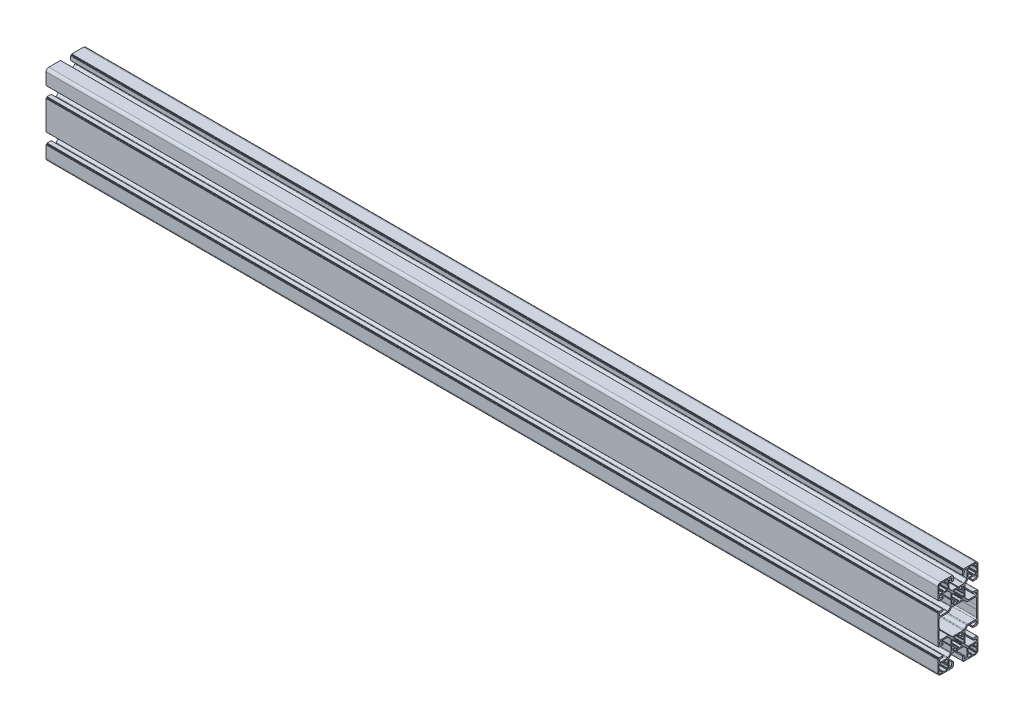
SolidWorks part; units mm, degrees
ref_plane "Спереди" through (0, 0, 0) normal (0, 0, 1) x (1, 0, 0)
ref_plane "Сверху" through (0, 0, 0) normal (0, 1, 0) x (1, 0, 0)
ref_plane "Справа" through (0, 0, 0) normal (1, 0, 0) x (0, 0, -1)
other "Центр тяжести"
sketch "Эскиз1" plane through (0, 0, 0) normal (0, 0, 1) x (1, 0, 0)
  line L0 (-35.8248, 14.5782) -> (-35.8248, 11.29)
  line L1 (-36.0902, 10.889) -> (-36.2238, 10.889)
  line L2 (-36.4238, 10.689) -> (-36.4238, 10.5554)
  line L3 (-36.8248, 10.29) -> (-40.1131, 10.29)
  line L4 (-40.3597, 10.4989) -> (-40.49, 11.2811)
  line L5 (-40.7366, 11.49) -> (-41.3131, 11.49)
  line L6 (-41.5597, 11.2811) -> (-41.69, 10.4989)
  line L7 (-41.9366, 10.29) -> (-44.8248, 10.29)
  line L8 (-45.2259, 10.5554) -> (-45.2259, 10.689)
  line L9 (-45.4259, 10.889) -> (-45.5595, 10.889)
  line L10 (-45.8248, 11.29) -> (-45.8248, 14.5948)
  line L11 (-45.6355, 14.8374) -> (-45.2142, 14.9427)
  line L12 (-45.0248, 15.1852) -> (-45.0248, 15.7948)
  line L13 (-45.2142, 16.0374) -> (-45.6355, 16.1427)
  line L14 (-45.8248, 16.3852) -> (-45.8248, 18.49)
  line L15 (-45.3992, 19.4567) -> (-45.1916, 19.4567)
  line L16 (-44.9916, 19.6567) -> (-44.9916, 19.8644)
  line L17 (-44.0248, 20.29) -> (-41.92, 20.29)
  line L18 (-41.6775, 20.1007) -> (-41.5722, 19.6794)
  line L19 (-41.3297, 19.49) -> (-40.72, 19.49)
  line L20 (-40.4775, 19.6794) -> (-40.3722, 20.1007)
  line L21 (-40.1297, 20.29) -> (-36.8248, 20.29)
  line L22 (-36.4238, 20.0247) -> (-36.4238, 19.8911)
  line L23 (-36.2238, 19.6911) -> (-36.0902, 19.6911)
  line L24 (-35.8248, 19.29) -> (-35.8248, 16.4018)
  line L25 (-36.0337, 16.1552) -> (-36.8159, 16.0248)
  line L26 (-37.0248, 15.7782) -> (-37.0248, 15.2018)
  line L27 (-36.8159, 14.9552) -> (-36.0337, 14.8248)
  line L28 (-40.1131, -12.31) -> (-36.8248, -12.31)
  line L29 (-36.4238, -12.5753) -> (-36.4238, -12.7089)
  line L30 (-36.2238, -12.9089) -> (-36.0902, -12.9089)
  line L31 (-35.8248, -13.31) -> (-35.8248, -16.5982)
  line L32 (-36.0337, -16.8448) -> (-36.8159, -16.9752)
  line L33 (-37.0248, -17.2218) -> (-37.0248, -17.7982)
  line L34 (-36.8159, -18.0448) -> (-36.0337, -18.1752)
  line L35 (-35.8248, -18.4218) -> (-35.8248, -21.31)
  line L36 (-36.0902, -21.711) -> (-36.2238, -21.711)
  line L37 (-36.4238, -21.911) -> (-36.4238, -22.0446)
  line L38 (-36.8248, -22.31) -> (-40.1297, -22.31)
  line L39 (-40.3722, -22.1206) -> (-40.4775, -21.6993)
  line L40 (-40.72, -21.51) -> (-41.3297, -21.51)
  line L41 (-41.5722, -21.6993) -> (-41.6775, -22.1206)
  line L42 (-41.92, -22.31) -> (-44.0248, -22.31)
  line L43 (-44.9916, -21.8843) -> (-44.9916, -21.6767)
  line L44 (-45.1916, -21.4767) -> (-45.3992, -21.4767)
  line L45 (-45.8248, -20.51) -> (-45.8248, -18.4052)
  line L46 (-45.6355, -18.1626) -> (-45.2142, -18.0573)
  line L47 (-45.0248, -17.8148) -> (-45.0248, -17.2052)
  line L48 (-45.2142, -16.9626) -> (-45.6355, -16.8573)
  line L49 (-45.8248, -16.6148) -> (-45.8248, -13.31)
  line L50 (-45.5595, -12.9089) -> (-45.4259, -12.9089)
  line L51 (-45.2259, -12.7089) -> (-45.2259, -12.5753)
  line L52 (-44.8248, -12.31) -> (-41.9366, -12.31)
  line L53 (-41.69, -12.5189) -> (-41.5597, -13.3011)
  line L54 (-41.3131, -13.51) -> (-40.7366, -13.51)
  line L55 (-40.49, -13.3011) -> (-40.3597, -12.5189)
  line L56 (-13.0248, 18.59) -> (-13.0248, 9.7264)
  line L57 (-13.4349, 8.7365) -> (-16.1148, 6.0566)
  line L58 (-16.5248, 5.0666) -> (-16.5248, -7.0866)
  line L59 (-16.1148, -8.0765) -> (-13.4349, -10.7564)
  line L60 (-13.0248, -11.7464) -> (-13.0248, -20.61)
  line L61 (-11.6248, -22.01) -> (-4.0497, -22.01)
  line L62 (0, -22.01) -> (7.5752, -22.01)
  line L63 (8.9752, -20.61) -> (8.9752, -11.7464)
  line L64 (9.3852, -10.7564) -> (12.0651, -8.0765)
  line L65 (12.4752, -7.0866) -> (12.4752, 5.0666)
  line L66 (12.0651, 6.0566) -> (9.3852, 8.7365)
  line L67 (8.9752, 9.7264) -> (8.9752, 18.59)
  line L68 (7.5752, 19.99) -> (0, 19.99)
  line L69 (-4.0497, 19.99) -> (-11.6248, 19.99)
  line L70 (32.7752, 10.29) -> (36.0634, 10.29)
  line L71 (36.31, 10.4989) -> (36.4403, 11.2811)
  line L72 (36.6869, 11.49) -> (37.2634, 11.49)
  line L73 (37.51, 11.2811) -> (37.6403, 10.4989)
  line L74 (37.8869, 10.29) -> (40.7752, 10.29)
  line L75 (41.1762, 10.5554) -> (41.1762, 10.689)
  line L76 (41.3762, 10.889) -> (41.5098, 10.889)
  line L77 (41.7752, 11.29) -> (41.7752, 14.5948)
  line L78 (41.5858, 14.8374) -> (41.1645, 14.9427)
  line L79 (40.9752, 15.1852) -> (40.9752, 15.7948)
  line L80 (41.1645, 16.0374) -> (41.5858, 16.1427)
  line L81 (41.7752, 16.3852) -> (41.7752, 18.49)
  line L82 (41.3495, 19.4567) -> (41.1419, 19.4567)
  line L83 (40.9419, 19.6567) -> (40.9419, 19.8644)
  line L84 (39.9752, 20.29) -> (37.8703, 20.29)
  line L85 (37.6278, 20.1007) -> (37.5225, 19.6794)
  line L86 (37.28, 19.49) -> (36.6703, 19.49)
  line L87 (36.4278, 19.6794) -> (36.3225, 20.1007)
  line L88 (36.08, 20.29) -> (32.7752, 20.29)
  line L89 (32.3741, 20.0247) -> (32.3741, 19.8911)
  line L90 (32.1741, 19.6911) -> (32.0405, 19.6911)
  line L91 (31.7752, 19.29) -> (31.7752, 16.4018)
  line L92 (31.9841, 16.1552) -> (32.7663, 16.0248)
  line L93 (32.9752, 15.7782) -> (32.9752, 15.2018)
  line L94 (32.7663, 14.9552) -> (31.9841, 14.8248)
  line L95 (31.7752, 14.5782) -> (31.7752, 11.29)
  line L96 (32.0405, 10.889) -> (32.1741, 10.889)
  line L97 (32.3741, 10.689) -> (32.3741, 10.5554)
  line L98 (32.7752, -12.31) -> (36.0634, -12.31)
  line L99 (36.31, -12.5189) -> (36.4403, -13.3011)
  line L100 (36.6869, -13.51) -> (37.2634, -13.51)
  line L101 (37.51, -13.3011) -> (37.6403, -12.5189)
  line L102 (37.8869, -12.31) -> (40.7752, -12.31)
  line L103 (41.1762, -12.5753) -> (41.1762, -12.7089)
  line L104 (41.3762, -12.9089) -> (41.5098, -12.9089)
  line L105 (41.7752, -13.31) -> (41.7752, -16.6148)
  line L106 (41.5858, -16.8573) -> (41.1645, -16.9626)
  line L107 (40.9752, -17.2052) -> (40.9752, -17.8148)
  line L108 (41.1645, -18.0573) -> (41.5858, -18.1626)
  line L109 (41.7752, -18.4052) -> (41.7752, -20.51)
  line L110 (41.3495, -21.4767) -> (41.1419, -21.4767)
  line L111 (40.9419, -21.6767) -> (40.9419, -21.8843)
  line L112 (39.9752, -22.31) -> (37.8703, -22.31)
  line L113 (37.6278, -22.1206) -> (37.5225, -21.6993)
  line L114 (37.28, -21.51) -> (36.6703, -21.51)
  line L115 (36.4278, -21.6993) -> (36.3225, -22.1206)
  line L116 (36.08, -22.31) -> (32.7752, -22.31)
  line L117 (32.3741, -22.0446) -> (32.3741, -21.911)
  line L118 (32.1741, -21.711) -> (32.0405, -21.711)
  line L119 (31.7752, -21.31) -> (31.7752, -18.4218)
  line L120 (31.9841, -18.1752) -> (32.7663, -18.0448)
  line L121 (32.9752, -17.7982) -> (32.9752, -17.2218)
  line L122 (32.7663, -16.9752) -> (31.9841, -16.8448)
  line L123 (31.7752, -16.5982) -> (31.7752, -13.31)
  line L124 (32.0405, -12.9089) -> (32.1741, -12.9089)
  line L125 (32.3741, -12.7089) -> (32.3741, -12.5753)
  line L138 (-18.1998, -23.51) -> (14.1502, -23.51)
  line L139 (14.4002, -23.26) -> (14.4002, -22.61)
  line L140 (14.5002, -22.51) -> (15.0752, -22.51)
  line L141 (15.3252, -22.26) -> (15.3252, -17.76)
  line L142 (15.0752, -17.51) -> (13.9794, -17.51)
  line L143 (13.7344, -17.7101) -> (13.0305, -21.1695)
  line L144 (12.2465, -21.81) -> (11.1752, -21.81)
  line L145 (10.3752, -21.01) -> (10.3752, -12.7263)
  line L146 (10.668, -12.0192) -> (13.3843, -9.3029)
  line L147 (14.0914, -9.01) -> (19.9447, -9.01)
  line L148 (20.0905, -8.9631) -> (20.4168, -8.7287)
  line L149 (20.5335, -8.7287) -> (20.8598, -8.9631)
  line L150 (21.0056, -9.01) -> (26.8589, -9.01)
  line L151 (27.566, -9.3029) -> (30.2823, -12.0192)
  line L152 (30.5752, -12.7263) -> (30.5752, -21.01)
  line L153 (29.7752, -21.81) -> (28.7038, -21.81)
  line L154 (27.9198, -21.1695) -> (27.2159, -17.7101)
  line L155 (26.9709, -17.51) -> (25.8752, -17.51)
  line L156 (25.6252, -17.76) -> (25.6252, -22.26)
  line L157 (25.8752, -22.51) -> (26.4502, -22.51)
  line L158 (26.5502, -22.61) -> (26.5502, -23.26)
  line L159 (26.8002, -23.51) -> (39.9752, -23.51)
  line L160 (42.9752, -20.51) -> (42.9752, -7.335)
  line L161 (42.7252, -7.085) -> (42.0752, -7.085)
  line L162 (41.9752, -6.985) -> (41.9752, -6.41)
  line L163 (41.7252, -6.16) -> (37.2252, -6.16)
  line L164 (36.9752, -6.41) -> (36.9752, -7.5057)
  line L165 (37.1753, -7.7507) -> (40.6347, -8.4546)
  line L166 (41.2752, -9.2386) -> (41.2752, -10.31)
  line L167 (40.4752, -11.11) -> (32.1914, -11.11)
  line L168 (31.4843, -10.8171) -> (28.768, -8.1008)
  line L169 (28.4752, -7.3937) -> (28.4752, -1.5404)
  line L170 (28.4282, -1.3946) -> (28.1939, -1.0683)
  line L171 (28.1939, -0.9517) -> (28.4282, -0.6253)
  line L172 (28.4752, -0.4795) -> (28.4752, 5.3737)
  line L173 (28.768, 6.0808) -> (31.4843, 8.7971)
  line L174 (32.1914, 9.09) -> (40.4752, 9.09)
  line L175 (41.2752, 8.29) -> (41.2752, 7.2186)
  line L176 (40.6347, 6.4347) -> (37.1753, 5.7308)
  line L177 (36.9752, 5.4858) -> (36.9752, 4.39)
  line L178 (37.2252, 4.14) -> (41.7252, 4.14)
  line L179 (41.9752, 4.39) -> (41.9752, 4.965)
  line L180 (42.0752, 5.065) -> (42.7252, 5.065)
  line L181 (42.9752, 5.315) -> (42.9752, 18.49)
  line L182 (39.9752, 21.49) -> (26.8002, 21.49)
  line L183 (26.5502, 21.24) -> (26.5502, 20.59)
  line L184 (26.4502, 20.49) -> (25.8752, 20.49)
  line L185 (25.6252, 20.24) -> (25.6252, 15.74)
  line L186 (25.8752, 15.49) -> (26.9709, 15.49)
  line L187 (27.2159, 15.6902) -> (27.9198, 19.1495)
  line L188 (28.7038, 19.79) -> (29.7752, 19.79)
  line L189 (30.5752, 18.99) -> (30.5752, 10.7063)
  line L190 (30.2823, 9.9992) -> (27.566, 7.2829)
  line L191 (26.8589, 6.99) -> (21.0056, 6.99)
  line L192 (20.8598, 6.9431) -> (20.5335, 6.7088)
  line L193 (20.4168, 6.7088) -> (20.0905, 6.9431)
  line L194 (19.9447, 6.99) -> (14.0914, 6.99)
  line L195 (13.3843, 7.2829) -> (10.668, 9.9992)
  line L196 (10.3752, 10.7063) -> (10.3752, 18.99)
  line L197 (11.1752, 19.79) -> (12.2465, 19.79)
  line L198 (13.0305, 19.1495) -> (13.7344, 15.6902)
  line L199 (13.9794, 15.49) -> (15.0752, 15.49)
  line L200 (15.3252, 15.74) -> (15.3252, 20.24)
  line L201 (15.0752, 20.49) -> (14.5002, 20.49)
  line L202 (14.4002, 20.59) -> (14.4002, 21.24)
  line L203 (14.1502, 21.49) -> (-18.1998, 21.49)
  line L204 (-18.4498, 21.24) -> (-18.4498, 20.59)
  line L205 (-18.5498, 20.49) -> (-19.1248, 20.49)
  line L206 (-19.3748, 20.24) -> (-19.3748, 15.74)
  line L207 (-19.1248, 15.49) -> (-18.0291, 15.49)
  line L208 (-17.7841, 15.6902) -> (-17.0802, 19.1495)
  line L209 (-16.2962, 19.79) -> (-15.2248, 19.79)
  line L210 (-14.4248, 18.99) -> (-14.4248, 10.7063)
  line L211 (-14.7177, 9.9992) -> (-17.434, 7.2829)
  line L212 (-18.1411, 6.99) -> (-23.9944, 6.99)
  line L213 (-24.1402, 6.9431) -> (-24.4665, 6.7088)
  line L214 (-24.5832, 6.7088) -> (-24.9095, 6.9431)
  line L215 (-25.0553, 6.99) -> (-30.9086, 6.99)
  line L216 (-31.6157, 7.2829) -> (-34.332, 9.9992)
  line L217 (-34.6248, 10.7063) -> (-34.6248, 18.99)
  line L218 (-33.8248, 19.79) -> (-32.7535, 19.79)
  line L219 (-31.9695, 19.1495) -> (-31.2656, 15.6902)
  line L220 (-31.0206, 15.49) -> (-29.9248, 15.49)
  line L221 (-29.6748, 15.74) -> (-29.6748, 20.24)
  line L222 (-29.9248, 20.49) -> (-30.4998, 20.49)
  line L223 (-30.5998, 20.59) -> (-30.5998, 21.24)
  line L224 (-30.8498, 21.49) -> (-44.0248, 21.49)
  line L225 (-47.0248, 18.49) -> (-47.0248, 5.315)
  line L226 (-46.7748, 5.065) -> (-46.1248, 5.065)
  line L227 (-46.0248, 4.965) -> (-46.0248, 4.39)
  line L228 (-45.7748, 4.14) -> (-41.2748, 4.14)
  line L229 (-41.0248, 4.39) -> (-41.0248, 5.4858)
  line L230 (-41.225, 5.7308) -> (-44.6844, 6.4347)
  line L231 (-45.3248, 7.2186) -> (-45.3248, 8.29)
  line L232 (-44.5248, 9.09) -> (-36.2411, 9.09)
  line L233 (-35.534, 8.7971) -> (-32.8177, 6.0808)
  line L234 (-32.5248, 5.3737) -> (-32.5248, -0.4795)
  line L235 (-32.4779, -0.6253) -> (-32.2436, -0.9517)
  line L236 (-32.2436, -1.0683) -> (-32.4779, -1.3946)
  line L237 (-32.5248, -1.5404) -> (-32.5248, -7.3937)
  line L238 (-32.8177, -8.1008) -> (-35.534, -10.8171)
  line L239 (-36.2411, -11.11) -> (-44.5248, -11.11)
  line L240 (-45.3248, -10.31) -> (-45.3248, -9.2386)
  line L241 (-44.6844, -8.4546) -> (-41.225, -7.7507)
  line L242 (-41.0248, -7.5057) -> (-41.0248, -6.41)
  line L243 (-41.2748, -6.16) -> (-45.7748, -6.16)
  line L244 (-46.0248, -6.41) -> (-46.0248, -6.985)
  line L245 (-46.1248, -7.085) -> (-46.7748, -7.085)
  line L246 (-47.0248, -7.335) -> (-47.0248, -20.51)
  line L247 (-44.0248, -23.51) -> (-30.8498, -23.51)
  line L248 (-30.5998, -23.26) -> (-30.5998, -22.61)
  line L249 (-30.4998, -22.51) -> (-29.9248, -22.51)
  line L250 (-29.6748, -22.26) -> (-29.6748, -17.76)
  line L251 (-29.9248, -17.51) -> (-31.0206, -17.51)
  line L252 (-31.2656, -17.7101) -> (-31.9695, -21.1695)
  line L253 (-32.7535, -21.81) -> (-33.8248, -21.81)
  line L254 (-34.6248, -21.01) -> (-34.6248, -12.7263)
  line L255 (-34.332, -12.0192) -> (-31.6157, -9.3029)
  line L256 (-30.9086, -9.01) -> (-25.0553, -9.01)
  line L257 (-24.9095, -8.9631) -> (-24.5832, -8.7287)
  line L258 (-24.4665, -8.7287) -> (-24.1402, -8.9631)
  line L259 (-23.9944, -9.01) -> (-18.1411, -9.01)
  line L260 (-17.434, -9.3029) -> (-14.7177, -12.0192)
  line L261 (-14.4248, -12.7263) -> (-14.4248, -21.01)
  line L262 (-15.2248, -21.81) -> (-16.2962, -21.81)
  line L263 (-17.0802, -21.1695) -> (-17.7841, -17.7101)
  line L264 (-18.0291, -17.51) -> (-19.1248, -17.51)
  line L265 (-19.3748, -17.76) -> (-19.3748, -22.26)
  line L266 (-19.1248, -22.51) -> (-18.5498, -22.51)
  line L267 (-18.4498, -22.61) -> (-18.4498, -23.26)
  line L268 (-29.3671, -7.75) -> (-25.5348, -7.75)
  line L269 (-25.2379, -7.4926) -> (-25.0557, -6.2244)
  line L270 (-24.8082, -6.01) -> (-24.2415, -6.01)
  line L271 (-23.994, -6.2244) -> (-23.8118, -7.4926)
  line L272 (-23.5149, -7.75) -> (-19.6826, -7.75)
  line L273 (-19.4485, -7.2623) -> (-21.2028, -5.0738)
  line L274 (-21.1845, -4.7407) -> (-20.7941, -4.3503)
  line L275 (-20.461, -4.332) -> (-18.2725, -6.0863)
  line L276 (-17.7848, -5.8522) -> (-17.7848, -2.02)
  line L277 (-18.0422, -1.723) -> (-19.3104, -1.5408)
  line L278 (-19.5248, -1.2933) -> (-19.5248, -0.7266)
  line L279 (-19.3104, -0.4792) -> (-18.0422, -0.297)
  line L280 (-17.7848, 0) -> (-17.7848, 3.8323)
  line L281 (-18.2725, 4.0664) -> (-20.461, 2.3121)
  line L282 (-20.7941, 2.3304) -> (-21.1845, 2.7207)
  line L283 (-21.2028, 3.0539) -> (-19.4485, 5.2424)
  line L284 (-19.6826, 5.73) -> (-23.5149, 5.73)
  line L285 (-23.8118, 5.4727) -> (-23.994, 4.2045)
  line L286 (-24.2415, 3.99) -> (-24.8082, 3.99)
  line L287 (-25.0557, 4.2045) -> (-25.2379, 5.4727)
  line L288 (-25.5348, 5.73) -> (-29.3671, 5.73)
  line L289 (-29.6012, 5.2424) -> (-27.8469, 3.0539)
  line L290 (-27.8652, 2.7207) -> (-28.2556, 2.3304)
  line L291 (-28.5887, 2.3121) -> (-30.7772, 4.0664)
  line L292 (-31.2648, 3.8323) -> (-31.2648, 0)
  line L293 (-31.0075, -0.297) -> (-29.7393, -0.4792)
  line L294 (-29.5248, -0.7266) -> (-29.5248, -1.2933)
  line L295 (-29.7393, -1.5408) -> (-31.0075, -1.723)
  line L296 (-31.2648, -2.02) -> (-31.2648, -5.8522)
  line L297 (-30.7772, -6.0863) -> (-28.5887, -4.332)
  line L298 (-28.2556, -4.3503) -> (-27.8652, -4.7407)
  line L299 (-27.8469, -5.0738) -> (-29.6012, -7.2623)
  line L300 (15.6329, -7.75) -> (19.4652, -7.75)
  line L301 (19.7621, -7.4926) -> (19.9443, -6.2244)
  line L302 (20.1918, -6.01) -> (20.7585, -6.01)
  line L303 (21.006, -6.2244) -> (21.1882, -7.4926)
  line L304 (21.4851, -7.75) -> (25.3174, -7.75)
  line L305 (25.5515, -7.2623) -> (23.7972, -5.0738)
  line L306 (23.8155, -4.7407) -> (24.2059, -4.3503)
  line L307 (24.539, -4.332) -> (26.7275, -6.0863)
  line L308 (27.2152, -5.8522) -> (27.2152, -2.02)
  line L309 (26.9578, -1.723) -> (25.6896, -1.5408)
  line L310 (25.4752, -1.2933) -> (25.4752, -0.7266)
  line L311 (25.6896, -0.4792) -> (26.9578, -0.297)
  line L312 (27.2152, 0) -> (27.2152, 3.8323)
  line L313 (26.7275, 4.0664) -> (24.539, 2.3121)
  line L314 (24.2059, 2.3304) -> (23.8155, 2.7207)
  line L315 (23.7972, 3.0539) -> (25.5515, 5.2424)
  line L316 (25.3174, 5.73) -> (21.4851, 5.73)
  line L317 (21.1882, 5.4727) -> (21.006, 4.2045)
  line L318 (20.7585, 3.99) -> (20.1918, 3.99)
  line L319 (19.9443, 4.2045) -> (19.7621, 5.4727)
  line L320 (19.4652, 5.73) -> (15.6329, 5.73)
  line L321 (15.3988, 5.2424) -> (17.1531, 3.0539)
  line L322 (17.1348, 2.7207) -> (16.7444, 2.3304)
  line L323 (16.4113, 2.3121) -> (14.2228, 4.0664)
  line L324 (13.7352, 3.8323) -> (13.7352, 0)
  line L325 (13.9925, -0.297) -> (15.2607, -0.4792)
  line L326 (15.4752, -0.7266) -> (15.4752, -1.2933)
  line L327 (15.2607, -1.5408) -> (13.9925, -1.723)
  line L328 (13.7352, -2.02) -> (13.7352, -5.8522)
  line L329 (14.2228, -6.0863) -> (16.4113, -4.332)
  line L330 (16.7444, -4.3503) -> (17.1348, -4.7407)
  line L331 (17.1531, -5.0738) -> (15.3988, -7.2623)
  arc A0 (-35.8453, 11.0886) -> (-35.8248, 11.29) centre (-36.8248, 11.29) ccw
  arc A1 (-36.0902, 10.889) -> (-35.8453, 11.0886) centre (-36.0902, 11.139) ccw
  arc A2 (-36.2238, 10.889) -> (-36.4238, 10.689) centre (-36.2238, 10.689) ccw
  arc A3 (-36.6235, 10.3105) -> (-36.4238, 10.5554) centre (-36.6738, 10.5554) ccw
  arc A4 (-36.8248, 10.29) -> (-36.6235, 10.3105) centre (-36.8248, 11.29) ccw
  arc A5 (-40.3597, 10.4989) -> (-40.1131, 10.29) centre (-40.1131, 10.54) ccw
  arc A6 (-40.49, 11.2811) -> (-40.7366, 11.49) centre (-40.7366, 11.24) ccw
  arc A7 (-41.3131, 11.49) -> (-41.5597, 11.2811) centre (-41.3131, 11.24) ccw
  arc A8 (-41.9366, 10.29) -> (-41.69, 10.4989) centre (-41.9366, 10.54) ccw
  arc A9 (-45.0262, 10.3105) -> (-44.8248, 10.29) centre (-44.8248, 11.29) ccw
  arc A10 (-45.2259, 10.5554) -> (-45.0262, 10.3105) centre (-44.9759, 10.5554) ccw
  arc A11 (-45.2259, 10.689) -> (-45.4259, 10.889) centre (-45.4259, 10.689) ccw
  arc A12 (-45.8044, 11.0886) -> (-45.5595, 10.889) centre (-45.5595, 11.139) ccw
  arc A13 (-45.8248, 11.29) -> (-45.8044, 11.0886) centre (-44.8248, 11.29) ccw
  arc A14 (-45.6355, 14.8374) -> (-45.8248, 14.5948) centre (-45.5748, 14.5948) ccw
  arc A15 (-45.2142, 14.9427) -> (-45.0248, 15.1852) centre (-45.2748, 15.1852) ccw
  arc A16 (-45.0248, 15.7948) -> (-45.2142, 16.0374) centre (-45.2748, 15.7948) ccw
  arc A17 (-45.8248, 16.3852) -> (-45.6355, 16.1427) centre (-45.5748, 16.3852) ccw
  arc A18 (-45.6209, 19.3223) -> (-45.8248, 18.49) centre (-44.0248, 18.49) ccw
  arc A19 (-45.3992, 19.4567) -> (-45.6209, 19.3223) centre (-45.3992, 19.2067) ccw
  arc A20 (-45.1916, 19.4567) -> (-44.9916, 19.6567) centre (-45.1916, 19.6567) ccw
  arc A21 (-44.8572, 20.086) -> (-44.9916, 19.8644) centre (-44.7416, 19.8644) ccw
  arc A22 (-44.0248, 20.29) -> (-44.8572, 20.086) centre (-44.0248, 18.49) ccw
  arc A23 (-41.6775, 20.1007) -> (-41.92, 20.29) centre (-41.92, 20.04) ccw
  arc A24 (-41.5722, 19.6794) -> (-41.3297, 19.49) centre (-41.3297, 19.74) ccw
  arc A25 (-40.72, 19.49) -> (-40.4775, 19.6794) centre (-40.72, 19.74) ccw
  arc A26 (-40.1297, 20.29) -> (-40.3722, 20.1007) centre (-40.1297, 20.04) ccw
  arc A27 (-36.6235, 20.2695) -> (-36.8248, 20.29) centre (-36.8248, 19.29) ccw
  arc A28 (-36.4238, 20.0247) -> (-36.6235, 20.2695) centre (-36.6738, 20.0247) ccw
  arc A29 (-36.4238, 19.8911) -> (-36.2238, 19.6911) centre (-36.2238, 19.8911) ccw
  arc A30 (-35.8453, 19.4914) -> (-36.0902, 19.6911) centre (-36.0902, 19.4411) ccw
  arc A31 (-35.8248, 19.29) -> (-35.8453, 19.4914) centre (-36.8248, 19.29) ccw
  arc A32 (-36.0337, 16.1552) -> (-35.8248, 16.4018) centre (-36.0748, 16.4018) ccw
  arc A33 (-36.8159, 16.0248) -> (-37.0248, 15.7782) centre (-36.7748, 15.7782) ccw
  arc A34 (-37.0248, 15.2018) -> (-36.8159, 14.9552) centre (-36.7748, 15.2018) ccw
  arc A35 (-35.8248, 14.5782) -> (-36.0337, 14.8248) centre (-36.0748, 14.5782) ccw
  arc A36 (-36.6235, -12.3305) -> (-36.8248, -12.31) centre (-36.8248, -13.31) ccw
  arc A37 (-36.4238, -12.5753) -> (-36.6235, -12.3305) centre (-36.6738, -12.5753) ccw
  arc A38 (-36.4238, -12.7089) -> (-36.2238, -12.9089) centre (-36.2238, -12.7089) ccw
  arc A39 (-35.8453, -13.1086) -> (-36.0902, -12.9089) centre (-36.0902, -13.1589) ccw
  arc A40 (-35.8248, -13.31) -> (-35.8453, -13.1086) centre (-36.8248, -13.31) ccw
  arc A41 (-36.0337, -16.8448) -> (-35.8248, -16.5982) centre (-36.0748, -16.5982) ccw
  arc A42 (-36.8159, -16.9752) -> (-37.0248, -17.2218) centre (-36.7748, -17.2218) ccw
  arc A43 (-37.0248, -17.7982) -> (-36.8159, -18.0448) centre (-36.7748, -17.7982) ccw
  arc A44 (-35.8248, -18.4218) -> (-36.0337, -18.1752) centre (-36.0748, -18.4218) ccw
  arc A45 (-35.8453, -21.5114) -> (-35.8248, -21.31) centre (-36.8248, -21.31) ccw
  arc A46 (-36.0902, -21.711) -> (-35.8453, -21.5114) centre (-36.0902, -21.461) ccw
  arc A47 (-36.2238, -21.711) -> (-36.4238, -21.911) centre (-36.2238, -21.911) ccw
  arc A48 (-36.6235, -22.2895) -> (-36.4238, -22.0446) centre (-36.6738, -22.0446) ccw
  arc A49 (-36.8248, -22.31) -> (-36.6235, -22.2895) centre (-36.8248, -21.31) ccw
  arc A50 (-40.3722, -22.1206) -> (-40.1297, -22.31) centre (-40.1297, -22.06) ccw
  arc A51 (-40.4775, -21.6993) -> (-40.72, -21.51) centre (-40.72, -21.76) ccw
  arc A52 (-41.3297, -21.51) -> (-41.5722, -21.6993) centre (-41.3297, -21.76) ccw
  arc A53 (-41.92, -22.31) -> (-41.6775, -22.1206) centre (-41.92, -22.06) ccw
  arc A54 (-44.8572, -22.106) -> (-44.0248, -22.31) centre (-44.0248, -20.51) ccw
  arc A55 (-44.9916, -21.8843) -> (-44.8572, -22.106) centre (-44.7416, -21.8843) ccw
  arc A56 (-44.9916, -21.6767) -> (-45.1916, -21.4767) centre (-45.1916, -21.6767) ccw
  arc A57 (-45.6209, -21.3423) -> (-45.3992, -21.4767) centre (-45.3992, -21.2267) ccw
  arc A58 (-45.8248, -20.51) -> (-45.6209, -21.3423) centre (-44.0248, -20.51) ccw
  arc A59 (-45.6355, -18.1626) -> (-45.8248, -18.4052) centre (-45.5748, -18.4052) ccw
  arc A60 (-45.2142, -18.0573) -> (-45.0248, -17.8148) centre (-45.2748, -17.8148) ccw
  arc A61 (-45.0248, -17.2052) -> (-45.2142, -16.9626) centre (-45.2748, -17.2052) ccw
  arc A62 (-45.8248, -16.6148) -> (-45.6355, -16.8573) centre (-45.5748, -16.6148) ccw
  arc A63 (-45.8044, -13.1086) -> (-45.8248, -13.31) centre (-44.8248, -13.31) ccw
  arc A64 (-45.5595, -12.9089) -> (-45.8044, -13.1086) centre (-45.5595, -13.1589) ccw
  arc A65 (-45.4259, -12.9089) -> (-45.2259, -12.7089) centre (-45.4259, -12.7089) ccw
  arc A66 (-45.0262, -12.3305) -> (-45.2259, -12.5753) centre (-44.9759, -12.5753) ccw
  arc A67 (-44.8248, -12.31) -> (-45.0262, -12.3305) centre (-44.8248, -13.31) ccw
  arc A68 (-41.69, -12.5189) -> (-41.9366, -12.31) centre (-41.9366, -12.56) ccw
  arc A69 (-41.5597, -13.3011) -> (-41.3131, -13.51) centre (-41.3131, -13.26) ccw
  arc A70 (-40.7366, -13.51) -> (-40.49, -13.3011) centre (-40.7366, -13.26) ccw
  arc A71 (-40.1131, -12.31) -> (-40.3597, -12.5189) centre (-40.1131, -12.56) ccw
  arc A72 (-13.4349, 8.7365) -> (-13.0248, 9.7264) centre (-14.4248, 9.7264) ccw
  arc A73 (-16.1148, 6.0566) -> (-16.5248, 5.0666) centre (-15.1248, 5.0666) ccw
  arc A74 (-16.5248, -7.0866) -> (-16.1148, -8.0765) centre (-15.1248, -7.0866) ccw
  arc A75 (-13.0248, -11.7464) -> (-13.4349, -10.7564) centre (-14.4248, -11.7464) ccw
  arc A76 (-13.0248, -20.61) -> (-11.6248, -22.01) centre (-11.6248, -20.61) ccw
  arc A77 (-4.0497, -22.01) -> (-4.001, -22.004) centre (-4.0497, -21.81) ccw
  arc A78 (-0.0486, -22.004) -> (-4.001, -22.004) centre (-2.0248, -29.885) ccw
  arc A79 (-0.0486, -22.004) -> (0, -22.01) centre (0, -21.81) ccw
  arc A80 (7.5752, -22.01) -> (8.9752, -20.61) centre (7.5752, -20.61) ccw
  arc A81 (9.3852, -10.7564) -> (8.9752, -11.7464) centre (10.3752, -11.7464) ccw
  arc A82 (12.0651, -8.0765) -> (12.4752, -7.0866) centre (11.0752, -7.0866) ccw
  arc A83 (12.4752, 5.0666) -> (12.0651, 6.0566) centre (11.0752, 5.0666) ccw
  arc A84 (8.9752, 9.7264) -> (9.3852, 8.7365) centre (10.3752, 9.7264) ccw
  arc A85 (8.9752, 18.59) -> (7.5752, 19.99) centre (7.5752, 18.59) ccw
  arc A86 (0, 19.99) -> (-0.0486, 19.984) centre (0, 19.79) ccw
  arc A87 (-4.001, 19.984) -> (-0.0486, 19.984) centre (-2.0248, 27.865) ccw
  arc A88 (-4.001, 19.984) -> (-4.0497, 19.99) centre (-4.0497, 19.79) ccw
  arc A89 (-11.6248, 19.99) -> (-13.0248, 18.59) centre (-11.6248, 18.59) ccw
  arc A90 (36.0634, 10.29) -> (36.31, 10.4989) centre (36.0634, 10.54) ccw
  arc A91 (36.6869, 11.49) -> (36.4403, 11.2811) centre (36.6869, 11.24) ccw
  arc A92 (37.51, 11.2811) -> (37.2634, 11.49) centre (37.2634, 11.24) ccw
  arc A93 (37.6403, 10.4989) -> (37.8869, 10.29) centre (37.8869, 10.54) ccw
  arc A94 (40.7752, 10.29) -> (40.9765, 10.3105) centre (40.7752, 11.29) ccw
  arc A95 (40.9765, 10.3105) -> (41.1762, 10.5554) centre (40.9262, 10.5554) ccw
  arc A96 (41.3762, 10.889) -> (41.1762, 10.689) centre (41.3762, 10.689) ccw
  arc A97 (41.5098, 10.889) -> (41.7547, 11.0886) centre (41.5098, 11.139) ccw
  arc A98 (41.7547, 11.0886) -> (41.7752, 11.29) centre (40.7752, 11.29) ccw
  arc A99 (41.7752, 14.5948) -> (41.5858, 14.8374) centre (41.5252, 14.5948) ccw
  arc A100 (40.9752, 15.1852) -> (41.1645, 14.9427) centre (41.2252, 15.1852) ccw
  arc A101 (41.1645, 16.0374) -> (40.9752, 15.7948) centre (41.2252, 15.7948) ccw
  arc A102 (41.5858, 16.1427) -> (41.7752, 16.3852) centre (41.5252, 16.3852) ccw
  arc A103 (41.7752, 18.49) -> (41.5712, 19.3223) centre (39.9752, 18.49) ccw
  arc A104 (41.5712, 19.3223) -> (41.3495, 19.4567) centre (41.3495, 19.2067) ccw
  arc A105 (40.9419, 19.6567) -> (41.1419, 19.4567) centre (41.1419, 19.6567) ccw
  arc A106 (40.9419, 19.8644) -> (40.8075, 20.086) centre (40.6919, 19.8644) ccw
  arc A107 (40.8075, 20.086) -> (39.9752, 20.29) centre (39.9752, 18.49) ccw
  arc A108 (37.8703, 20.29) -> (37.6278, 20.1007) centre (37.8703, 20.04) ccw
  arc A109 (37.28, 19.49) -> (37.5225, 19.6794) centre (37.28, 19.74) ccw
  arc A110 (36.4278, 19.6794) -> (36.6703, 19.49) centre (36.6703, 19.74) ccw
  arc A111 (36.3225, 20.1007) -> (36.08, 20.29) centre (36.08, 20.04) ccw
  arc A112 (32.7752, 20.29) -> (32.5738, 20.2695) centre (32.7752, 19.29) ccw
  arc A113 (32.5738, 20.2695) -> (32.3741, 20.0247) centre (32.6241, 20.0247) ccw
  arc A114 (32.1741, 19.6911) -> (32.3741, 19.8911) centre (32.1741, 19.8911) ccw
  arc A115 (32.0405, 19.6911) -> (31.7956, 19.4914) centre (32.0405, 19.4411) ccw
  arc A116 (31.7956, 19.4914) -> (31.7752, 19.29) centre (32.7752, 19.29) ccw
  arc A117 (31.7752, 16.4018) -> (31.9841, 16.1552) centre (32.0252, 16.4018) ccw
  arc A118 (32.9752, 15.7782) -> (32.7663, 16.0248) centre (32.7252, 15.7782) ccw
  arc A119 (32.7663, 14.9552) -> (32.9752, 15.2018) centre (32.7252, 15.2018) ccw
  arc A120 (31.9841, 14.8248) -> (31.7752, 14.5782) centre (32.0252, 14.5782) ccw
  arc A121 (31.7752, 11.29) -> (31.7956, 11.0886) centre (32.7752, 11.29) ccw
  arc A122 (31.7956, 11.0886) -> (32.0405, 10.889) centre (32.0405, 11.139) ccw
  arc A123 (32.3741, 10.689) -> (32.1741, 10.889) centre (32.1741, 10.689) ccw
  arc A124 (32.3741, 10.5554) -> (32.5738, 10.3105) centre (32.6241, 10.5554) ccw
  arc A125 (32.5738, 10.3105) -> (32.7752, 10.29) centre (32.7752, 11.29) ccw
  arc A126 (36.31, -12.5189) -> (36.0634, -12.31) centre (36.0634, -12.56) ccw
  arc A127 (36.4403, -13.3011) -> (36.6869, -13.51) centre (36.6869, -13.26) ccw
  arc A128 (37.2634, -13.51) -> (37.51, -13.3011) centre (37.2634, -13.26) ccw
  arc A129 (37.8869, -12.31) -> (37.6403, -12.5189) centre (37.8869, -12.56) ccw
  arc A130 (40.9765, -12.3305) -> (40.7752, -12.31) centre (40.7752, -13.31) ccw
  arc A131 (41.1762, -12.5753) -> (40.9765, -12.3305) centre (40.9262, -12.5753) ccw
  arc A132 (41.1762, -12.7089) -> (41.3762, -12.9089) centre (41.3762, -12.7089) ccw
  arc A133 (41.7547, -13.1086) -> (41.5098, -12.9089) centre (41.5098, -13.1589) ccw
  arc A134 (41.7752, -13.31) -> (41.7547, -13.1086) centre (40.7752, -13.31) ccw
  arc A135 (41.5858, -16.8573) -> (41.7752, -16.6148) centre (41.5252, -16.6148) ccw
  arc A136 (41.1645, -16.9626) -> (40.9752, -17.2052) centre (41.2252, -17.2052) ccw
  arc A137 (40.9752, -17.8148) -> (41.1645, -18.0573) centre (41.2252, -17.8148) ccw
  arc A138 (41.7752, -18.4052) -> (41.5858, -18.1626) centre (41.5252, -18.4052) ccw
  arc A139 (41.5712, -21.3423) -> (41.7752, -20.51) centre (39.9752, -20.51) ccw
  arc A140 (41.3495, -21.4767) -> (41.5712, -21.3423) centre (41.3495, -21.2267) ccw
  arc A141 (41.1419, -21.4767) -> (40.9419, -21.6767) centre (41.1419, -21.6767) ccw
  arc A142 (40.8075, -22.106) -> (40.9419, -21.8843) centre (40.6919, -21.8843) ccw
  arc A143 (39.9752, -22.31) -> (40.8075, -22.106) centre (39.9752, -20.51) ccw
  arc A144 (37.6278, -22.1206) -> (37.8703, -22.31) centre (37.8703, -22.06) ccw
  arc A145 (37.5225, -21.6993) -> (37.28, -21.51) centre (37.28, -21.76) ccw
  arc A146 (36.6703, -21.51) -> (36.4278, -21.6993) centre (36.6703, -21.76) ccw
  arc A147 (36.08, -22.31) -> (36.3225, -22.1206) centre (36.08, -22.06) ccw
  arc A148 (32.5738, -22.2895) -> (32.7752, -22.31) centre (32.7752, -21.31) ccw
  arc A149 (32.3741, -22.0446) -> (32.5738, -22.2895) centre (32.6241, -22.0446) ccw
  arc A150 (32.3741, -21.911) -> (32.1741, -21.711) centre (32.1741, -21.911) ccw
  arc A151 (31.7956, -21.5114) -> (32.0405, -21.711) centre (32.0405, -21.461) ccw
  arc A152 (31.7752, -21.31) -> (31.7956, -21.5114) centre (32.7752, -21.31) ccw
  arc A153 (31.9841, -18.1752) -> (31.7752, -18.4218) centre (32.0252, -18.4218) ccw
  arc A154 (32.7663, -18.0448) -> (32.9752, -17.7982) centre (32.7252, -17.7982) ccw
  arc A155 (32.9752, -17.2218) -> (32.7663, -16.9752) centre (32.7252, -17.2218) ccw
  arc A156 (31.7752, -16.5982) -> (31.9841, -16.8448) centre (32.0252, -16.5982) ccw
  arc A157 (31.7956, -13.1086) -> (31.7752, -13.31) centre (32.7752, -13.31) ccw
  arc A158 (32.0405, -12.9089) -> (31.7956, -13.1086) centre (32.0405, -13.1589) ccw
  arc A159 (32.1741, -12.9089) -> (32.3741, -12.7089) centre (32.1741, -12.7089) ccw
  arc A160 (32.5738, -12.3305) -> (32.3741, -12.5753) centre (32.6241, -12.5753) ccw
  arc A161 (32.7752, -12.31) -> (32.5738, -12.3305) centre (32.7752, -13.31) ccw
  arc A170 (14.1502, -23.51) -> (14.4002, -23.26) centre (14.1502, -23.26) ccw
  arc A171 (14.5002, -22.51) -> (14.4002, -22.61) centre (14.5002, -22.61) ccw
  arc A172 (15.0752, -22.51) -> (15.3252, -22.26) centre (15.0752, -22.26) ccw
  arc A173 (15.3252, -17.76) -> (15.0752, -17.51) centre (15.0752, -17.76) ccw
  arc A174 (13.9794, -17.51) -> (13.7344, -17.7101) centre (13.9794, -17.76) ccw
  arc A175 (12.2465, -21.81) -> (13.0305, -21.1695) centre (12.2465, -21.01) ccw
  arc A176 (10.3752, -21.01) -> (11.1752, -21.81) centre (11.1752, -21.01) ccw
  arc A177 (10.668, -12.0192) -> (10.3752, -12.7263) centre (11.3752, -12.7263) ccw
  arc A178 (14.0914, -9.01) -> (13.3843, -9.3029) centre (14.0914, -10.01) ccw
  arc A179 (19.9447, -9.01) -> (20.0905, -8.9631) centre (19.9447, -8.76) ccw
  arc A180 (20.5335, -8.7287) -> (20.4168, -8.7287) centre (20.4752, -8.81) ccw
  arc A181 (20.8598, -8.9631) -> (21.0056, -9.01) centre (21.0056, -8.76) ccw
  arc A182 (27.566, -9.3029) -> (26.8589, -9.01) centre (26.8589, -10.01) ccw
  arc A183 (30.5752, -12.7263) -> (30.2823, -12.0192) centre (29.5752, -12.7263) ccw
  arc A184 (29.7752, -21.81) -> (30.5752, -21.01) centre (29.7752, -21.01) ccw
  arc A185 (27.9198, -21.1695) -> (28.7038, -21.81) centre (28.7038, -21.01) ccw
  arc A186 (27.2159, -17.7101) -> (26.9709, -17.51) centre (26.9709, -17.76) ccw
  arc A187 (25.8752, -17.51) -> (25.6252, -17.76) centre (25.8752, -17.76) ccw
  arc A188 (25.6252, -22.26) -> (25.8752, -22.51) centre (25.8752, -22.26) ccw
  arc A189 (26.5502, -22.61) -> (26.4502, -22.51) centre (26.4502, -22.61) ccw
  arc A190 (26.5502, -23.26) -> (26.8002, -23.51) centre (26.8002, -23.26) ccw
  arc A191 (39.9752, -23.51) -> (42.9752, -20.51) centre (39.9752, -20.51) ccw
  arc A192 (42.9752, -7.335) -> (42.7252, -7.085) centre (42.7252, -7.335) ccw
  arc A193 (41.9752, -6.985) -> (42.0752, -7.085) centre (42.0752, -6.985) ccw
  arc A194 (41.9752, -6.41) -> (41.7252, -6.16) centre (41.7252, -6.41) ccw
  arc A195 (37.2252, -6.16) -> (36.9752, -6.41) centre (37.2252, -6.41) ccw
  arc A196 (36.9752, -7.5057) -> (37.1753, -7.7507) centre (37.2252, -7.5057) ccw
  arc A197 (41.2752, -9.2386) -> (40.6347, -8.4546) centre (40.4752, -9.2386) ccw
  arc A198 (40.4752, -11.11) -> (41.2752, -10.31) centre (40.4752, -10.31) ccw
  arc A199 (31.4843, -10.8171) -> (32.1914, -11.11) centre (32.1914, -10.11) ccw
  arc A200 (28.4752, -7.3937) -> (28.768, -8.1008) centre (29.4752, -7.3937) ccw
  arc A201 (28.4752, -1.5404) -> (28.4282, -1.3946) centre (28.2252, -1.5404) ccw
  arc A202 (28.1939, -0.9517) -> (28.1939, -1.0683) centre (28.2752, -1.01) ccw
  arc A203 (28.4282, -0.6253) -> (28.4752, -0.4795) centre (28.2252, -0.4795) ccw
  arc A204 (28.768, 6.0808) -> (28.4752, 5.3737) centre (29.4752, 5.3737) ccw
  arc A205 (32.1914, 9.09) -> (31.4843, 8.7971) centre (32.1914, 8.09) ccw
  arc A206 (41.2752, 8.29) -> (40.4752, 9.09) centre (40.4752, 8.29) ccw
  arc A207 (40.6347, 6.4347) -> (41.2752, 7.2186) centre (40.4752, 7.2186) ccw
  arc A208 (37.1753, 5.7308) -> (36.9752, 5.4858) centre (37.2252, 5.4858) ccw
  arc A209 (36.9752, 4.39) -> (37.2252, 4.14) centre (37.2252, 4.39) ccw
  arc A210 (41.7252, 4.14) -> (41.9752, 4.39) centre (41.7252, 4.39) ccw
  arc A211 (42.0752, 5.065) -> (41.9752, 4.965) centre (42.0752, 4.965) ccw
  arc A212 (42.7252, 5.065) -> (42.9752, 5.315) centre (42.7252, 5.315) ccw
  arc A213 (42.9752, 18.49) -> (39.9752, 21.49) centre (39.9752, 18.49) ccw
  arc A214 (26.8002, 21.49) -> (26.5502, 21.24) centre (26.8002, 21.24) ccw
  arc A215 (26.4502, 20.49) -> (26.5502, 20.59) centre (26.4502, 20.59) ccw
  arc A216 (25.8752, 20.49) -> (25.6252, 20.24) centre (25.8752, 20.24) ccw
  arc A217 (25.6252, 15.74) -> (25.8752, 15.49) centre (25.8752, 15.74) ccw
  arc A218 (26.9709, 15.49) -> (27.2159, 15.6902) centre (26.9709, 15.74) ccw
  arc A219 (28.7038, 19.79) -> (27.9198, 19.1495) centre (28.7038, 18.99) ccw
  arc A220 (30.5752, 18.99) -> (29.7752, 19.79) centre (29.7752, 18.99) ccw
  arc A221 (30.2823, 9.9992) -> (30.5752, 10.7063) centre (29.5752, 10.7063) ccw
  arc A222 (26.8589, 6.99) -> (27.566, 7.2829) centre (26.8589, 7.99) ccw
  arc A223 (21.0056, 6.99) -> (20.8598, 6.9431) centre (21.0056, 6.74) ccw
  arc A224 (20.4168, 6.7088) -> (20.5335, 6.7088) centre (20.4752, 6.79) ccw
  arc A225 (20.0905, 6.9431) -> (19.9447, 6.99) centre (19.9447, 6.74) ccw
  arc A226 (13.3843, 7.2829) -> (14.0914, 6.99) centre (14.0914, 7.99) ccw
  arc A227 (10.3752, 10.7063) -> (10.668, 9.9992) centre (11.3752, 10.7063) ccw
  arc A228 (11.1752, 19.79) -> (10.3752, 18.99) centre (11.1752, 18.99) ccw
  arc A229 (13.0305, 19.1495) -> (12.2465, 19.79) centre (12.2465, 18.99) ccw
  arc A230 (13.7344, 15.6902) -> (13.9794, 15.49) centre (13.9794, 15.74) ccw
  arc A231 (15.0752, 15.49) -> (15.3252, 15.74) centre (15.0752, 15.74) ccw
  arc A232 (15.3252, 20.24) -> (15.0752, 20.49) centre (15.0752, 20.24) ccw
  arc A233 (14.4002, 20.59) -> (14.5002, 20.49) centre (14.5002, 20.59) ccw
  arc A234 (14.4002, 21.24) -> (14.1502, 21.49) centre (14.1502, 21.24) ccw
  arc A235 (-18.1998, 21.49) -> (-18.4498, 21.24) centre (-18.1998, 21.24) ccw
  arc A236 (-18.5498, 20.49) -> (-18.4498, 20.59) centre (-18.5498, 20.59) ccw
  arc A237 (-19.1248, 20.49) -> (-19.3748, 20.24) centre (-19.1248, 20.24) ccw
  arc A238 (-19.3748, 15.74) -> (-19.1248, 15.49) centre (-19.1248, 15.74) ccw
  arc A239 (-18.0291, 15.49) -> (-17.7841, 15.6902) centre (-18.0291, 15.74) ccw
  arc A240 (-16.2962, 19.79) -> (-17.0802, 19.1495) centre (-16.2962, 18.99) ccw
  arc A241 (-14.4248, 18.99) -> (-15.2248, 19.79) centre (-15.2248, 18.99) ccw
  arc A242 (-14.7177, 9.9992) -> (-14.4248, 10.7063) centre (-15.4248, 10.7063) ccw
  arc A243 (-18.1411, 6.99) -> (-17.434, 7.2829) centre (-18.1411, 7.99) ccw
  arc A244 (-23.9944, 6.99) -> (-24.1402, 6.9431) centre (-23.9944, 6.74) ccw
  arc A245 (-24.5832, 6.7088) -> (-24.4665, 6.7088) centre (-24.5248, 6.79) ccw
  arc A246 (-24.9095, 6.9431) -> (-25.0553, 6.99) centre (-25.0553, 6.74) ccw
  arc A247 (-31.6157, 7.2829) -> (-30.9086, 6.99) centre (-30.9086, 7.99) ccw
  arc A248 (-34.6248, 10.7063) -> (-34.332, 9.9992) centre (-33.6248, 10.7063) ccw
  arc A249 (-33.8248, 19.79) -> (-34.6248, 18.99) centre (-33.8248, 18.99) ccw
  arc A250 (-31.9695, 19.1495) -> (-32.7535, 19.79) centre (-32.7535, 18.99) ccw
  arc A251 (-31.2656, 15.6902) -> (-31.0206, 15.49) centre (-31.0206, 15.74) ccw
  arc A252 (-29.9248, 15.49) -> (-29.6748, 15.74) centre (-29.9248, 15.74) ccw
  arc A253 (-29.6748, 20.24) -> (-29.9248, 20.49) centre (-29.9248, 20.24) ccw
  arc A254 (-30.5998, 20.59) -> (-30.4998, 20.49) centre (-30.4998, 20.59) ccw
  arc A255 (-30.5998, 21.24) -> (-30.8498, 21.49) centre (-30.8498, 21.24) ccw
  arc A256 (-44.0248, 21.49) -> (-47.0248, 18.49) centre (-44.0248, 18.49) ccw
  arc A257 (-47.0248, 5.315) -> (-46.7748, 5.065) centre (-46.7748, 5.315) ccw
  arc A258 (-46.0248, 4.965) -> (-46.1248, 5.065) centre (-46.1248, 4.965) ccw
  arc A259 (-46.0248, 4.39) -> (-45.7748, 4.14) centre (-45.7748, 4.39) ccw
  arc A260 (-41.2748, 4.14) -> (-41.0248, 4.39) centre (-41.2748, 4.39) ccw
  arc A261 (-41.0248, 5.4858) -> (-41.225, 5.7308) centre (-41.2748, 5.4858) ccw
  arc A262 (-45.3248, 7.2186) -> (-44.6844, 6.4347) centre (-44.5248, 7.2186) ccw
  arc A263 (-44.5248, 9.09) -> (-45.3248, 8.29) centre (-44.5248, 8.29) ccw
  arc A264 (-35.534, 8.7971) -> (-36.2411, 9.09) centre (-36.2411, 8.09) ccw
  arc A265 (-32.5248, 5.3737) -> (-32.8177, 6.0808) centre (-33.5248, 5.3737) ccw
  arc A266 (-32.5248, -0.4795) -> (-32.4779, -0.6253) centre (-32.2748, -0.4795) ccw
  arc A267 (-32.2436, -1.0683) -> (-32.2436, -0.9517) centre (-32.3248, -1.01) ccw
  arc A268 (-32.4779, -1.3946) -> (-32.5248, -1.5404) centre (-32.2748, -1.5404) ccw
  arc A269 (-32.8177, -8.1008) -> (-32.5248, -7.3937) centre (-33.5248, -7.3937) ccw
  arc A270 (-36.2411, -11.11) -> (-35.534, -10.8171) centre (-36.2411, -10.11) ccw
  arc A271 (-45.3248, -10.31) -> (-44.5248, -11.11) centre (-44.5248, -10.31) ccw
  arc A272 (-44.6844, -8.4546) -> (-45.3248, -9.2386) centre (-44.5248, -9.2386) ccw
  arc A273 (-41.225, -7.7507) -> (-41.0248, -7.5057) centre (-41.2748, -7.5057) ccw
  arc A274 (-41.0248, -6.41) -> (-41.2748, -6.16) centre (-41.2748, -6.41) ccw
  arc A275 (-45.7748, -6.16) -> (-46.0248, -6.41) centre (-45.7748, -6.41) ccw
  arc A276 (-46.1248, -7.085) -> (-46.0248, -6.985) centre (-46.1248, -6.985) ccw
  arc A277 (-46.7748, -7.085) -> (-47.0248, -7.335) centre (-46.7748, -7.335) ccw
  arc A278 (-47.0248, -20.51) -> (-44.0248, -23.51) centre (-44.0248, -20.51) ccw
  arc A279 (-30.8498, -23.51) -> (-30.5998, -23.26) centre (-30.8498, -23.26) ccw
  arc A280 (-30.4998, -22.51) -> (-30.5998, -22.61) centre (-30.4998, -22.61) ccw
  arc A281 (-29.9248, -22.51) -> (-29.6748, -22.26) centre (-29.9248, -22.26) ccw
  arc A282 (-29.6748, -17.76) -> (-29.9248, -17.51) centre (-29.9248, -17.76) ccw
  arc A283 (-31.0206, -17.51) -> (-31.2656, -17.7101) centre (-31.0206, -17.76) ccw
  arc A284 (-32.7535, -21.81) -> (-31.9695, -21.1695) centre (-32.7535, -21.01) ccw
  arc A285 (-34.6248, -21.01) -> (-33.8248, -21.81) centre (-33.8248, -21.01) ccw
  arc A286 (-34.332, -12.0192) -> (-34.6248, -12.7263) centre (-33.6248, -12.7263) ccw
  arc A287 (-30.9086, -9.01) -> (-31.6157, -9.3029) centre (-30.9086, -10.01) ccw
  arc A288 (-25.0553, -9.01) -> (-24.9095, -8.9631) centre (-25.0553, -8.76) ccw
  arc A289 (-24.4665, -8.7287) -> (-24.5832, -8.7287) centre (-24.5248, -8.81) ccw
  arc A290 (-24.1402, -8.9631) -> (-23.9944, -9.01) centre (-23.9944, -8.76) ccw
  arc A291 (-17.434, -9.3029) -> (-18.1411, -9.01) centre (-18.1411, -10.01) ccw
  arc A292 (-14.4248, -12.7263) -> (-14.7177, -12.0192) centre (-15.4248, -12.7263) ccw
  arc A293 (-15.2248, -21.81) -> (-14.4248, -21.01) centre (-15.2248, -21.01) ccw
  arc A294 (-17.0802, -21.1695) -> (-16.2962, -21.81) centre (-16.2962, -21.01) ccw
  arc A295 (-17.7841, -17.7101) -> (-18.0291, -17.51) centre (-18.0291, -17.76) ccw
  arc A296 (-19.1248, -17.51) -> (-19.3748, -17.76) centre (-19.1248, -17.76) ccw
  arc A297 (-19.3748, -22.26) -> (-19.1248, -22.51) centre (-19.1248, -22.26) ccw
  arc A298 (-18.4498, -22.61) -> (-18.5498, -22.51) centre (-18.5498, -22.61) ccw
  arc A299 (-18.4498, -23.26) -> (-18.1998, -23.51) centre (-18.1998, -23.26) ccw
  arc A300 (-25.5348, -7.75) -> (-25.2379, -7.4926) centre (-25.5348, -7.45) ccw
  arc A301 (-24.8082, -6.01) -> (-25.0557, -6.2244) centre (-24.8082, -6.26) ccw
  arc A302 (-23.994, -6.2244) -> (-24.2415, -6.01) centre (-24.2415, -6.26) ccw
  arc A303 (-23.8118, -7.4926) -> (-23.5149, -7.75) centre (-23.5149, -7.45) ccw
  arc A304 (-19.6826, -7.75) -> (-19.4485, -7.2623) centre (-19.6826, -7.45) ccw
  arc A305 (-21.1845, -4.7407) -> (-21.2028, -5.0738) centre (-21.0077, -4.9175) ccw
  arc A306 (-20.461, -4.332) -> (-20.7941, -4.3503) centre (-20.6174, -4.5271) ccw
  arc A307 (-18.2725, -6.0863) -> (-17.7848, -5.8522) centre (-18.0848, -5.8522) ccw
  arc A308 (-17.7848, -2.02) -> (-18.0422, -1.723) centre (-18.0848, -2.02) ccw
  arc A309 (-19.5248, -1.2933) -> (-19.3104, -1.5408) centre (-19.2748, -1.2933) ccw
  arc A310 (-19.3104, -0.4792) -> (-19.5248, -0.7266) centre (-19.2748, -0.7266) ccw
  arc A311 (-18.0422, -0.297) -> (-17.7848, 0) centre (-18.0848, 0) ccw
  arc A312 (-17.7848, 3.8323) -> (-18.2725, 4.0664) centre (-18.0848, 3.8323) ccw
  arc A313 (-20.7941, 2.3304) -> (-20.461, 2.3121) centre (-20.6174, 2.5072) ccw
  arc A314 (-21.2028, 3.0539) -> (-21.1845, 2.7207) centre (-21.0077, 2.8975) ccw
  arc A315 (-19.4485, 5.2424) -> (-19.6826, 5.73) centre (-19.6826, 5.43) ccw
  arc A316 (-23.5149, 5.73) -> (-23.8118, 5.4727) centre (-23.5149, 5.43) ccw
  arc A317 (-24.2415, 3.99) -> (-23.994, 4.2045) centre (-24.2415, 4.24) ccw
  arc A318 (-25.0557, 4.2045) -> (-24.8082, 3.99) centre (-24.8082, 4.24) ccw
  arc A319 (-25.2379, 5.4727) -> (-25.5348, 5.73) centre (-25.5348, 5.43) ccw
  arc A320 (-29.3671, 5.73) -> (-29.6012, 5.2424) centre (-29.3671, 5.43) ccw
  arc A321 (-27.8652, 2.7207) -> (-27.8469, 3.0539) centre (-28.042, 2.8975) ccw
  arc A322 (-28.5887, 2.3121) -> (-28.2556, 2.3304) centre (-28.4323, 2.5072) ccw
  arc A323 (-30.7772, 4.0664) -> (-31.2648, 3.8323) centre (-30.9648, 3.8323) ccw
  arc A324 (-31.2648, 0) -> (-31.0075, -0.297) centre (-30.9648, 0) ccw
  arc A325 (-29.5248, -0.7266) -> (-29.7393, -0.4792) centre (-29.7748, -0.7266) ccw
  arc A326 (-29.7393, -1.5408) -> (-29.5248, -1.2933) centre (-29.7748, -1.2933) ccw
  arc A327 (-31.0075, -1.723) -> (-31.2648, -2.02) centre (-30.9648, -2.02) ccw
  arc A328 (-31.2648, -5.8522) -> (-30.7772, -6.0863) centre (-30.9648, -5.8522) ccw
  arc A329 (-28.2556, -4.3503) -> (-28.5887, -4.332) centre (-28.4323, -4.5271) ccw
  arc A330 (-27.8469, -5.0738) -> (-27.8652, -4.7407) centre (-28.042, -4.9175) ccw
  arc A331 (-29.6012, -7.2623) -> (-29.3671, -7.75) centre (-29.3671, -7.45) ccw
  arc A332 (19.4652, -7.75) -> (19.7621, -7.4926) centre (19.4652, -7.45) ccw
  arc A333 (20.1918, -6.01) -> (19.9443, -6.2244) centre (20.1918, -6.26) ccw
  arc A334 (21.006, -6.2244) -> (20.7585, -6.01) centre (20.7585, -6.26) ccw
  arc A335 (21.1882, -7.4926) -> (21.4851, -7.75) centre (21.4851, -7.45) ccw
  arc A336 (25.3174, -7.75) -> (25.5515, -7.2623) centre (25.3174, -7.45) ccw
  arc A337 (23.8155, -4.7407) -> (23.7972, -5.0738) centre (23.9923, -4.9175) ccw
  arc A338 (24.539, -4.332) -> (24.2059, -4.3503) centre (24.3826, -4.5271) ccw
  arc A339 (26.7275, -6.0863) -> (27.2152, -5.8522) centre (26.9152, -5.8522) ccw
  arc A340 (27.2152, -2.02) -> (26.9578, -1.723) centre (26.9152, -2.02) ccw
  arc A341 (25.4752, -1.2933) -> (25.6896, -1.5408) centre (25.7252, -1.2933) ccw
  arc A342 (25.6896, -0.4792) -> (25.4752, -0.7266) centre (25.7252, -0.7266) ccw
  arc A343 (26.9578, -0.297) -> (27.2152, 0) centre (26.9152, 0) ccw
  arc A344 (27.2152, 3.8323) -> (26.7275, 4.0664) centre (26.9152, 3.8323) ccw
  arc A345 (24.2059, 2.3304) -> (24.539, 2.3121) centre (24.3826, 2.5072) ccw
  arc A346 (23.7972, 3.0539) -> (23.8155, 2.7207) centre (23.9923, 2.8975) ccw
  arc A347 (25.5515, 5.2424) -> (25.3174, 5.73) centre (25.3174, 5.43) ccw
  arc A348 (21.4851, 5.73) -> (21.1882, 5.4727) centre (21.4851, 5.43) ccw
  arc A349 (20.7585, 3.99) -> (21.006, 4.2045) centre (20.7585, 4.24) ccw
  arc A350 (19.9443, 4.2045) -> (20.1918, 3.99) centre (20.1918, 4.24) ccw
  arc A351 (19.7621, 5.4727) -> (19.4652, 5.73) centre (19.4652, 5.43) ccw
  arc A352 (15.6329, 5.73) -> (15.3988, 5.2424) centre (15.6329, 5.43) ccw
  arc A353 (17.1348, 2.7207) -> (17.1531, 3.0539) centre (16.958, 2.8975) ccw
  arc A354 (16.4113, 2.3121) -> (16.7444, 2.3304) centre (16.5677, 2.5072) ccw
  arc A355 (14.2228, 4.0664) -> (13.7352, 3.8323) centre (14.0352, 3.8323) ccw
  arc A356 (13.7352, 0) -> (13.9925, -0.297) centre (14.0352, 0) ccw
  arc A357 (15.4752, -0.7266) -> (15.2607, -0.4792) centre (15.2252, -0.7266) ccw
  arc A358 (15.2607, -1.5408) -> (15.4752, -1.2933) centre (15.2252, -1.2933) ccw
  arc A359 (13.9925, -1.723) -> (13.7352, -2.02) centre (14.0352, -2.02) ccw
  arc A360 (13.7352, -5.8522) -> (14.2228, -6.0863) centre (14.0352, -5.8522) ccw
  arc A361 (16.7444, -4.3503) -> (16.4113, -4.332) centre (16.5677, -4.5271) ccw
  arc A362 (17.1531, -5.0738) -> (17.1348, -4.7407) centre (16.958, -4.9175) ccw
  arc A363 (15.3988, -7.2623) -> (15.6329, -7.75) centre (15.6329, -7.45) ccw
extrude "Бобышка-Вытянуть1" add sketch "Эскиз1" along normal blind 1000
move or copy body "Тело-Переместить/Копировать1" bodies to move or copy 103 copy no rotation origin (-167.6799, -166.665, 334.3449) rotation axis (0.5774, 0.5774, 0.5774) rotation angle 120
